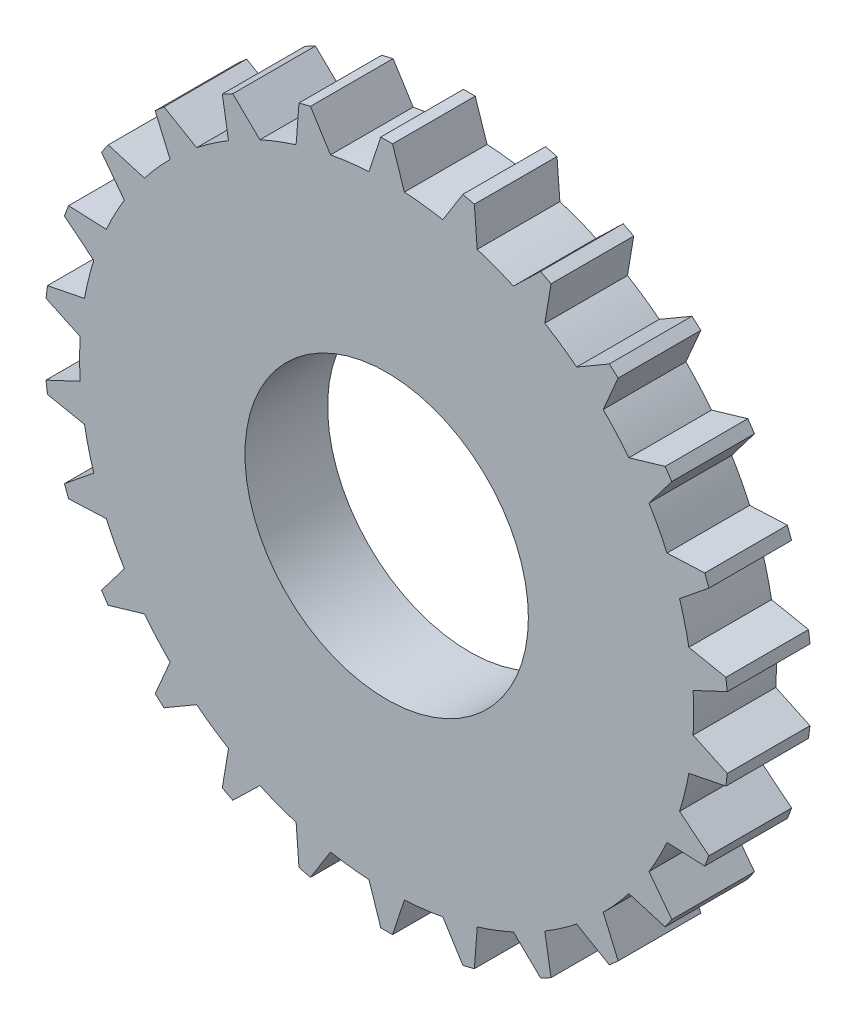
SolidWorks part; units mm, degrees
ref_plane "Front Plane" through (0, 0, 0) normal (0, 0, 1) x (1, 0, 0)
ref_plane "Top Plane" through (0, 0, 0) normal (0, 1, 0) x (1, 0, 0)
ref_plane "Right Plane" through (0, 0, 0) normal (1, 0, 0) x (0, 0, -1)
sketch "Sketch1" plane through (0, 0, 0) normal (0, 0, 1) x (1, 0, 0)
  line L0 (0, 0) -> (0, 21.7596) construction
  line L17 (6.4537, 28.2728) -> (4.7554, 25.5614)
  line L18 (6.4537, 28.2728) -> (7.4246, 28.0335)
  line L19 (7.4246, 28.0335) -> (7.6683, 24.8435)
  line L20 (13.0322, 25.9068) -> (10.7345, 23.6806)
  line L21 (13.0322, 25.9068) -> (13.9177, 25.442)
  line L22 (13.9177, 25.442) -> (13.3909, 22.2864)
  line L23 (18.8534, 22.0351) -> (16.0897, 20.4235)
  line L24 (18.8534, 22.0351) -> (19.602, 21.372)
  line L25 (19.602, 21.372) -> (18.3352, 18.4342)
  line L26 (23.579, 16.8829) -> (20.5098, 15.9796)
  line L27 (-1.5, 25.9567) -> (1.5, 25.9567) construction
  line L28 (-0.5, 28.9957) -> (0.5, 28.9957)
  line L29 (-0.5, 28.9957) -> (-1.5, 25.9567)
  line L30 (0.5, 28.9957) -> (1.5, 25.9567)
  line L31 (23.579, 16.8829) -> (24.147, 16.0599)
  line L32 (24.147, 16.0599) -> (22.214, 13.5106)
  line L33 (26.9341, 10.7495) -> (23.738, 10.6069)
  line L34 (26.9341, 10.7495) -> (27.2887, 9.8145)
  line L35 (27.2887, 9.8145) -> (24.8018, 7.8018)
  line L36 (28.724, 3.9914) -> (25.5866, 4.6178)
  line L37 (28.724, 3.9914) -> (28.8445, 2.9987)
  line L38 (28.8445, 2.9987) -> (25.9482, 1.6397)
  line L39 (28.8445, -2.9987) -> (25.9482, -1.6397)
  line L40 (28.8445, -2.9987) -> (28.724, -3.9914)
  line L41 (28.724, -3.9914) -> (25.5866, -4.6178)
  line L42 (27.2887, -9.8145) -> (24.8018, -7.8018)
  line L43 (27.2887, -9.8145) -> (26.9341, -10.7495)
  line L44 (26.9341, -10.7495) -> (23.738, -10.6069)
  line L45 (24.147, -16.0599) -> (22.214, -13.5106)
  line L46 (24.147, -16.0599) -> (23.579, -16.8829)
  line L47 (23.579, -16.8829) -> (20.5098, -15.9796)
  line L48 (19.602, -21.372) -> (18.3352, -18.4342)
  line L49 (19.602, -21.372) -> (18.8534, -22.0351)
  line L50 (18.8534, -22.0351) -> (16.0897, -20.4235)
  line L51 (13.9177, -25.442) -> (13.3909, -22.2864)
  line L52 (13.9177, -25.442) -> (13.0322, -25.9068)
  line L53 (13.0322, -25.9068) -> (10.7345, -23.6806)
  line L54 (7.4246, -28.0335) -> (7.6683, -24.8435)
  line L55 (7.4246, -28.0335) -> (6.4537, -28.2728)
  line L56 (6.4537, -28.2728) -> (4.7554, -25.5614)
  line L57 (0.5, -28.9957) -> (1.5, -25.9567)
  line L58 (0.5, -28.9957) -> (-0.5, -28.9957)
  line L59 (-0.5, -28.9957) -> (-1.5, -25.9567)
  line L60 (-6.4537, -28.2728) -> (-4.7554, -25.5614)
  line L61 (-6.4537, -28.2728) -> (-7.4246, -28.0335)
  line L62 (-7.4246, -28.0335) -> (-7.6683, -24.8435)
  line L63 (-13.0322, -25.9068) -> (-10.7345, -23.6806)
  line L64 (-13.0322, -25.9068) -> (-13.9177, -25.442)
  line L65 (-13.9177, -25.442) -> (-13.3909, -22.2864)
  line L66 (-18.8534, -22.0351) -> (-16.0897, -20.4235)
  line L67 (-18.8534, -22.0351) -> (-19.602, -21.372)
  line L68 (-19.602, -21.372) -> (-18.3352, -18.4342)
  line L69 (-23.579, -16.8829) -> (-20.5098, -15.9796)
  line L70 (-23.579, -16.8829) -> (-24.147, -16.0599)
  line L71 (-24.147, -16.0599) -> (-22.214, -13.5106)
  line L72 (-26.9341, -10.7495) -> (-23.738, -10.6069)
  line L73 (-26.9341, -10.7495) -> (-27.2887, -9.8145)
  line L74 (-27.2887, -9.8145) -> (-24.8018, -7.8018)
  line L75 (-28.724, -3.9914) -> (-25.5866, -4.6178)
  line L76 (-28.724, -3.9914) -> (-28.8445, -2.9987)
  line L77 (-28.8445, -2.9987) -> (-25.9482, -1.6397)
  line L78 (-28.8445, 2.9987) -> (-25.9482, 1.6397)
  line L79 (-28.8445, 2.9987) -> (-28.724, 3.9914)
  line L80 (-28.724, 3.9914) -> (-25.5866, 4.6178)
  line L81 (-27.2887, 9.8145) -> (-24.8018, 7.8018)
  line L82 (-27.2887, 9.8145) -> (-26.9341, 10.7495)
  line L83 (-26.9341, 10.7495) -> (-23.738, 10.6069)
  line L84 (-24.147, 16.0599) -> (-22.214, 13.5106)
  line L85 (-24.147, 16.0599) -> (-23.579, 16.8829)
  line L86 (-23.579, 16.8829) -> (-20.5098, 15.9796)
  line L87 (-19.602, 21.372) -> (-18.3352, 18.4342)
  line L88 (-19.602, 21.372) -> (-18.8534, 22.0351)
  line L89 (-18.8534, 22.0351) -> (-16.0897, 20.4235)
  line L90 (-13.9177, 25.442) -> (-13.3909, 22.2864)
  line L91 (-13.9177, 25.442) -> (-13.0322, 25.9068)
  line L92 (-13.0322, 25.9068) -> (-10.7345, 23.6806)
  line L93 (-7.4246, 28.0335) -> (-7.6683, 24.8435)
  line L94 (-7.4246, 28.0335) -> (-6.4537, 28.2728)
  line L95 (-6.4537, 28.2728) -> (-4.7554, 25.5614)
  circle A0 centre (0, 0) radius 12
  arc A17 (-1.5, 25.9567) -> (-4.7554, 25.5614) centre (0, 0) ccw
  arc A18 (-18.8534, 22.0351) -> (-19.602, 21.372) centre (0, 0) ccw construction
  arc A19 (4.7554, 25.5614) -> (1.5, 25.9567) centre (0, 0) ccw
  arc A20 (10.7345, 23.6806) -> (7.6683, 24.8435) centre (0, 0) ccw
  arc A21 (16.0897, 20.4235) -> (13.3909, 22.2864) centre (0, 0) ccw
  arc A22 (20.5098, 15.9796) -> (18.3352, 18.4342) centre (0, 0) ccw
  arc A23 (23.738, 10.6069) -> (22.214, 13.5106) centre (0, 0) ccw
  arc A24 (25.5866, 4.6178) -> (24.8018, 7.8018) centre (0, 0) ccw
  arc A25 (25.9482, -1.6397) -> (25.9482, 1.6397) centre (0, 0) ccw
  arc A26 (24.8018, -7.8018) -> (25.5866, -4.6178) centre (0, 0) ccw
  arc A27 (22.214, -13.5106) -> (23.738, -10.6069) centre (0, 0) ccw
  arc A28 (18.3352, -18.4342) -> (20.5098, -15.9796) centre (0, 0) ccw
  arc A29 (13.3909, -22.2864) -> (16.0897, -20.4235) centre (0, 0) ccw
  arc A30 (7.6683, -24.8435) -> (10.7345, -23.6806) centre (0, 0) ccw
  arc A31 (1.5, -25.9567) -> (4.7554, -25.5614) centre (0, 0) ccw
  arc A32 (-4.7554, -25.5614) -> (-1.5, -25.9567) centre (0, 0) ccw
  arc A33 (-10.7345, -23.6806) -> (-7.6683, -24.8435) centre (0, 0) ccw
  arc A34 (-16.0897, -20.4235) -> (-13.3909, -22.2864) centre (0, 0) ccw
  arc A35 (-20.5098, -15.9796) -> (-18.3352, -18.4342) centre (0, 0) ccw
  arc A36 (-23.738, -10.6069) -> (-22.214, -13.5106) centre (0, 0) ccw
  arc A37 (-25.5866, -4.6178) -> (-24.8018, -7.8018) centre (0, 0) ccw
  arc A38 (-25.9482, 1.6397) -> (-25.9482, -1.6397) centre (0, 0) ccw
  arc A39 (-24.8018, 7.8018) -> (-25.5866, 4.6178) centre (0, 0) ccw
  arc A40 (-22.214, 13.5106) -> (-23.738, 10.6069) centre (0, 0) ccw
  arc A41 (-18.3352, 18.4342) -> (-20.5098, 15.9796) centre (0, 0) ccw
  arc A42 (-13.3909, 22.2864) -> (-16.0897, 20.4235) centre (0, 0) ccw
  arc A43 (-7.6683, 24.8435) -> (-10.7345, 23.6806) centre (0, 0) ccw
  arc A44 (-13.0322, 25.9068) -> (-13.9177, 25.442) centre (0, 0) ccw construction
  arc A45 (-6.4537, 28.2728) -> (-7.4246, 28.0335) centre (0, 0) ccw construction
  arc A46 (7.4246, 28.0335) -> (-0.5, 28.9957) centre (0, 0) ccw construction
  arc A47 (13.9177, 25.442) -> (13.0322, 25.9068) centre (0, 0) ccw construction
  arc A48 (19.602, 21.372) -> (18.8534, 22.0351) centre (0, 0) ccw construction
  arc A49 (24.147, 16.0599) -> (23.579, 16.8829) centre (0, 0) ccw construction
  arc A50 (27.2887, 9.8145) -> (26.9341, 10.7495) centre (0, 0) ccw construction
  arc A51 (26.9341, -10.7495) -> (27.2887, -9.8145) centre (0, 0) ccw construction
  arc A52 (23.579, -16.8829) -> (24.147, -16.0599) centre (0, 0) ccw construction
  arc A53 (13.0322, -25.9068) -> (13.9177, -25.442) centre (0, 0) ccw construction
  arc A54 (18.8534, -22.0351) -> (19.602, -21.372) centre (0, 0) ccw construction
  arc A55 (-0.5, -28.9957) -> (0.5, -28.9957) centre (0, 0) ccw construction
  arc A56 (6.4537, -28.2728) -> (7.4246, -28.0335) centre (0, 0) ccw construction
  arc A57 (-7.4246, -28.0335) -> (-6.4537, -28.2728) centre (0, 0) ccw construction
  arc A58 (-13.9177, -25.442) -> (-13.0322, -25.9068) centre (0, 0) ccw construction
  arc A59 (-19.602, -21.372) -> (-18.8534, -22.0351) centre (0, 0) ccw construction
  arc A60 (-27.2887, -9.8145) -> (-26.9341, -10.7495) centre (0, 0) ccw construction
  arc A61 (-28.8445, -2.9987) -> (-28.724, -3.9914) centre (0, 0) ccw construction
  arc A62 (-28.724, 3.9914) -> (-28.8445, 2.9987) centre (0, 0) ccw construction
  arc A63 (-26.9341, 10.7495) -> (-27.2887, 9.8145) centre (0, 0) ccw construction
  arc A64 (-23.579, 16.8829) -> (-24.147, 16.0599) centre (0, 0) ccw construction
  arc A65 (-24.147, -16.0599) -> (-23.579, -16.8829) centre (0, 0) ccw construction
  arc A66 (28.8445, 2.9987) -> (28.724, 3.9914) centre (0, 0) ccw construction
  arc A67 (28.724, -3.9914) -> (28.8445, -2.9987) centre (0, 0) ccw construction
  point P41 (0, 0)
  point P112 (0, 0)
  dimension "D1" = 24
  dimension "D2" = 58
  dimension "D3" = 3
  dimension "D6" = 52
  dimension "D4" = 1.5
  dimension "D5" = 1.5
  dimension "D7" = 1
  dimension "D8" = 26
extrude "Boss-Extrude1" add sketch "Sketch1" along normal blind 7
